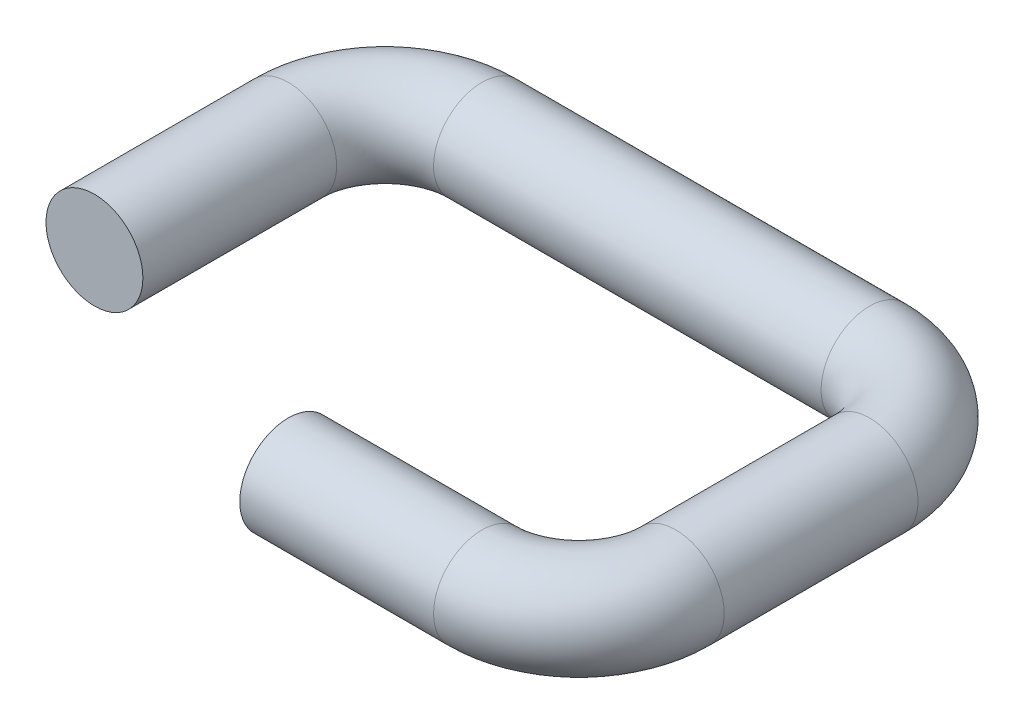
SolidWorks part; units mm, degrees
ref_plane "Front Plane" through (0, 0, 0) normal (0, 0, 1) x (1, 0, 0)
ref_plane "Top Plane" through (0, 0, 0) normal (0, 1, 0) x (1, 0, 0)
ref_plane "Right Plane" through (0, 0, 0) normal (1, 0, 0) x (0, 0, -1)
sketch "Sketch1" plane through (0, 0, 0) normal (0, 1, 0) x (1, 0, 0)
  line L0 (0, 0) -> (0, 10)
  line L1 (5, 15) -> (25, 15)
  line L2 (30, 10) -> (30, 0)
  line L3 (25, -5) -> (15, -5)
  arc A0 (30, 0) -> (25, -5) centre (25, 0) cw
  arc A1 (25, 15) -> (30, 10) centre (25, 10) cw
  arc A2 (0, 10) -> (5, 15) centre (5, 10) cw
  dimension "D5" = 5
  dimension "D1" = 30
  dimension "D2" = 15
  dimension "D3" = 20
  dimension "D4" = 15
sweep "Sweep1" add path "Sketch1" circular profile diameter 5 parameters "D3"=5
